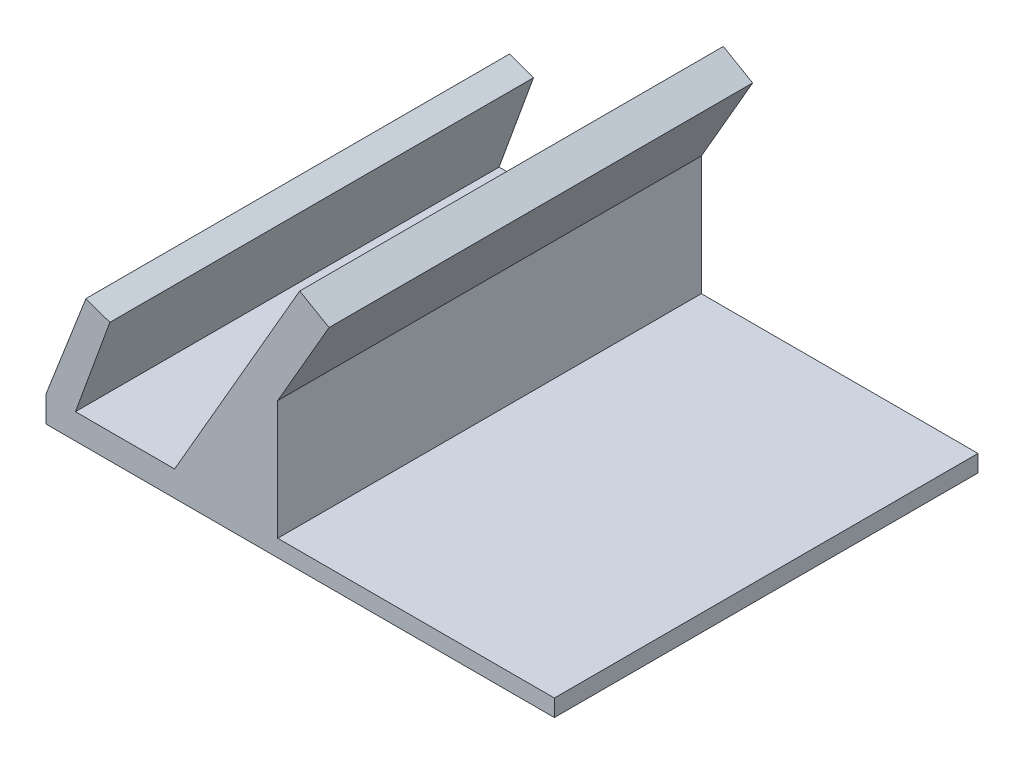
SolidWorks part; units mm, degrees
ref_plane "Alzado" through (0, 0, 0) normal (0, 0, 1) x (1, 0, 0)
ref_plane "Planta" through (0, 0, 0) normal (0, 1, 0) x (1, 0, 0)
ref_plane "Vista lateral" through (0, 0, 0) normal (1, 0, 0) x (0, 0, -1)
sketch "Croquis1" plane through (0, 0, 0) normal (0, 0, 1) x (1, 0, 0)
  line L0 (-84.4925, -6.9994) -> (-44.4925, -6.9994)
  line L1 (-44.4925, -6.9994) -> (-44.4925, -5.7386)
  line L2 (-84.4925, -6.9994) -> (-84.4925, -4.1096)
  line L3 (-84.4243, -3.7467) -> (-80.1293, 7.2806)
  line L4 (-84.4925, -3.9218) -> (-84.6143, -3.128) construction
  line L5 (-80.5307, -2.6574) -> (-81.0191, -3.9994)
  line L6 (-77.2974, 6.2261) -> (-80.5307, -2.6574)
  line L7 (-69.3132, -3.9994) -> (-81.0191, -3.9994)
  line L8 (-54.5499, 21.5714) -> (-69.3132, -3.9994)
  line L9 (-69.3132, -3.9994) -> (-69.3132, 10.4243) construction
  line L10 (-84.4925, -4.1096) -> (-84.4925, -3.9218)
  line L11 (-44.4925, -5.7386) -> (-44.4925, -4.9994)
  line L12 (-45.4925, -4.9994) -> (-57.1474, -4.9994)
  line L13 (-57.1474, -4.9994) -> (-57.1474, 9.0724)
  line L14 (-57.1474, 9.0724) -> (-51.5858, 18.7054)
  line L15 (-44.4925, -4.9994) -> (-45.4925, -4.9994)
  line L16 (-84.4925, -3.9218) -> (-84.4243, -3.7467)
  line L17 (-77.2974, 6.2261) -> (-76.9554, 7.1658)
  line L18 (-51.5858, 18.7054) -> (-51.0858, 19.5714)
  line L19 (-51.0858, 19.5714) -> (-54.5499, 21.5714)
  line L21 (-76.9554, 7.1658) -> (-79.7744, 8.1919)
  line L22 (-79.7744, 8.1919) -> (-80.1293, 7.2806)
  point P32 (-79.7744, 8.1919)
  dimension "D5" = 4
  dimension "D1" = 30
  dimension "D2" = 13
  dimension "D3" = 30
  dimension "D4" = 3
  dimension "D6" = 3
  dimension "D7" = 11.706
  dimension "D8" = 40
  dimension "D9" = 2
extrude "Saliente-Extruir1" add sketch "Croquis1" along normal blind 50
sketch "Croquis2" plane through (-44.4925, 0, 0) normal (1, 0, 0) x (0, 0, -1)
  line L1 (-50, -4.9994) -> (0, -4.9994)
  line L2 (-50, -4.9994) -> (-50, -6.9994)
  line L3 (-50, -6.9994) -> (0, -6.9994)
  line L4 (0, -4.9994) -> (0, -6.9994)
extrude "Saliente-Extruir2" add sketch "Croquis2" along normal blind 20
